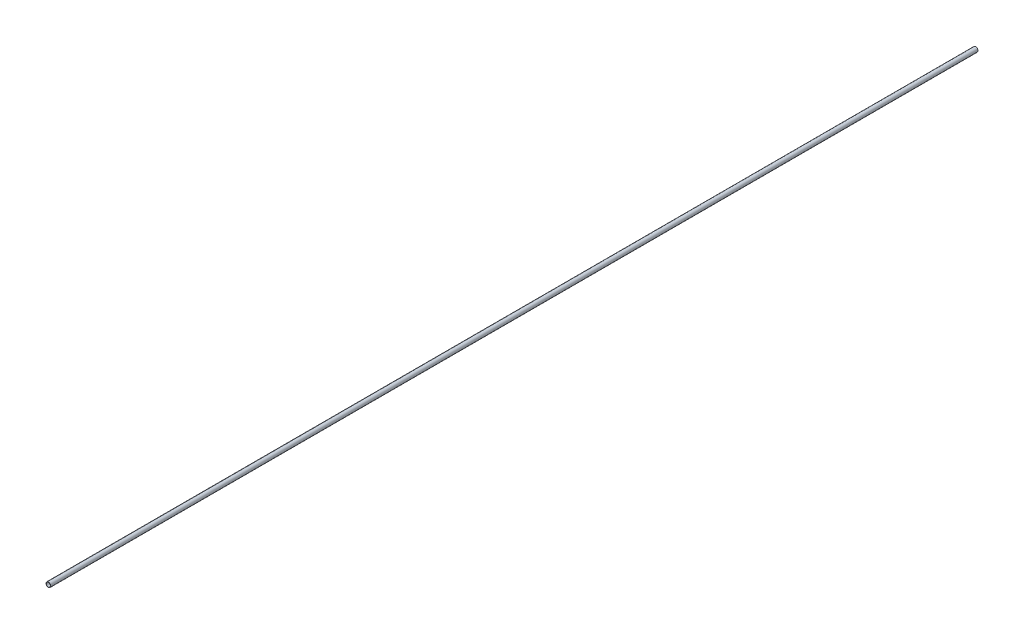
SolidWorks part; units mm, degrees
ref_plane "Front Plane" through (0, 0, 0) normal (0, 0, 1) x (1, 0, 0)
ref_plane "Top Plane" through (0, 0, 0) normal (0, 1, 0) x (1, 0, 0)
ref_plane "Right Plane" through (0, 0, 0) normal (1, 0, 0) x (0, 0, -1)
ref_plane "Plane1" through (0, 0, 0) normal (0, 0, -1) x (-1, 0, 0)
sketch "Sketch1" plane through (0, 0, 0) normal (0, 0, 1) x (1, 0, 0)
  circle A0 centre (0, 0) radius 2.23
  dimension "D1" = 4.46
extrude "Extrude-Thin1" add sketch "Sketch1" along normal blind 1000 thin
